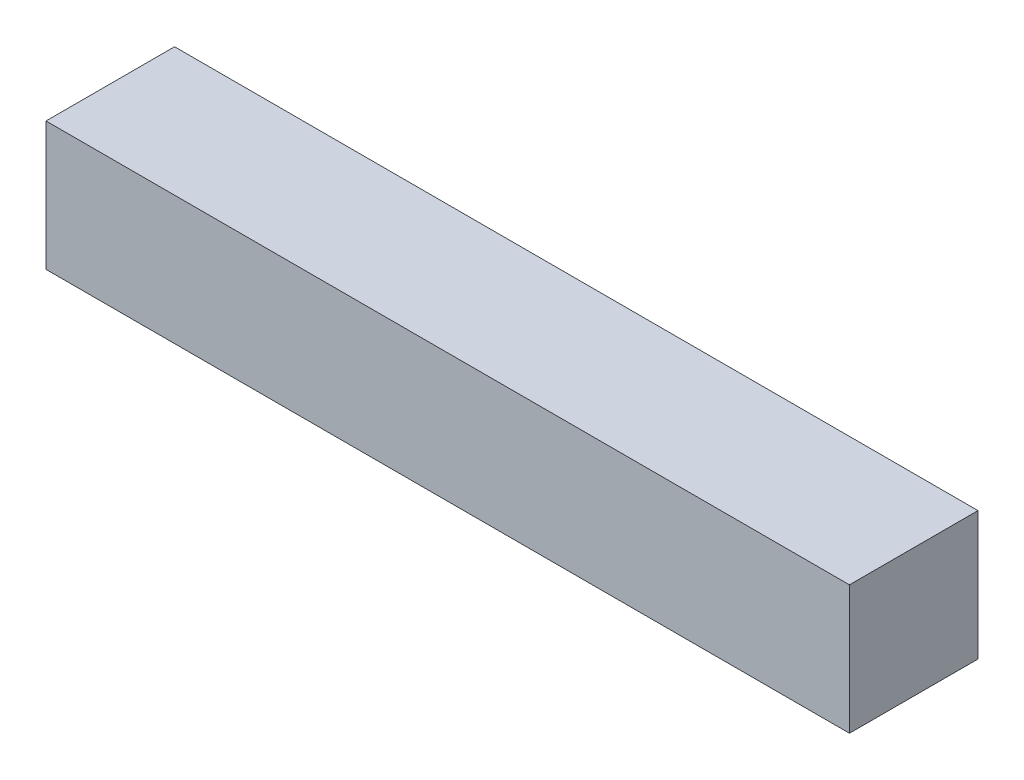
SolidWorks part; units mm, degrees
ref_plane "Front Plane" through (0, 0, 0) normal (0, 0, 1) x (1, 0, 0)
ref_plane "Top Plane" through (0, 0, 0) normal (0, 1, 0) x (1, 0, 0)
ref_plane "Right Plane" through (0, 0, 0) normal (1, 0, 0) x (0, 0, -1)
sketch "Sketch1" plane through (0, 0, 0) normal (0, 1, 0) x (1, 0, 0)
  line L1 (0, 0) -> (25, 0)
  line L2 (0, 0) -> (0, -4)
  line L3 (0, -4) -> (25, -4)
  line L4 (25, 0) -> (25, -4)
  dimension "D1" = 4
  dimension "D2" = 25
extrude "Boss-Extrude1" add sketch "Sketch1" along normal blind 4
